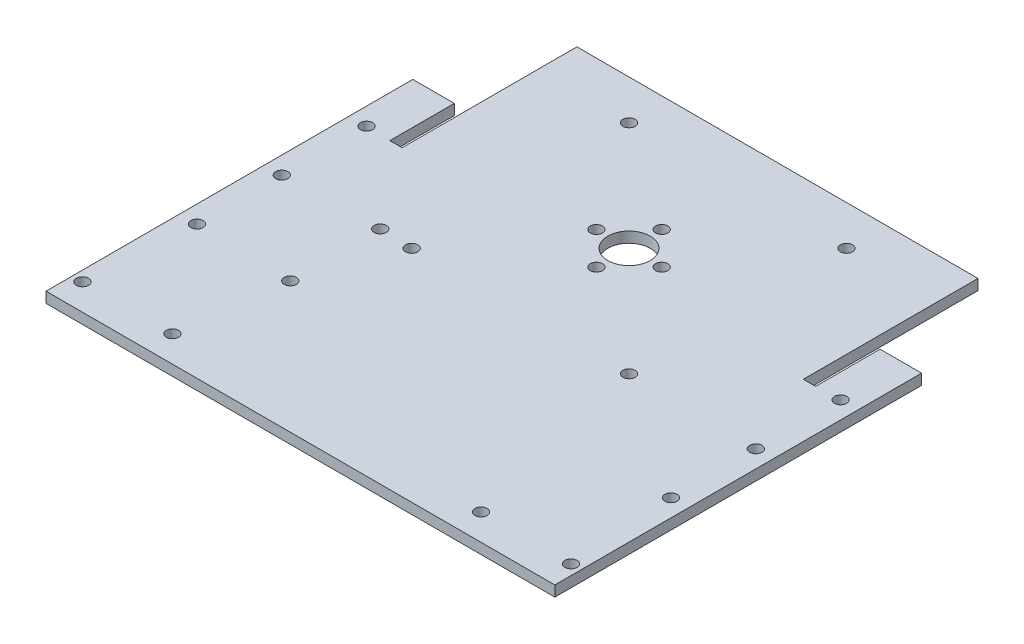
SolidWorks part; units mm, degrees
ref_plane "Front" through (0, 0, 0) normal (0, 0, 1) x (1, 0, 0)
ref_plane "Top" through (0, 0, 0) normal (0, 1, 0) x (1, 0, 0)
ref_plane "Right" through (0, 0, 0) normal (1, 0, 0) x (0, 0, -1)
sketch "Sketch1" plane through (0, 0, 0) normal (0, 1, 0) x (1, 0, 0)
  line L1 (76.2, -44.45) -> (-76.2, -44.45)
  line L2 (76.2, -44.45) -> (76.2, 44.45)
  line L3 (76.2, 44.45) -> (-76.2, 44.45)
  line L4 (-76.2, -44.45) -> (-76.2, 44.45)
  line L5 (76.2, -44.45) -> (-76.2, 44.45) construction
  line L6 (76.2, 44.45) -> (-76.2, -44.45) construction
  point P0 (0, 0)
  dimension "D1" = 88.9
  dimension "D2" = 152.4
extrude "Boss-Extrude1" add sketch "Sketch1" along normal blind 3.175
sketch "Sketch2" plane through (0, 3.175, 0) normal (0, 1, 0) x (1, 0, 0)
  line L0 (-76.2, 0) -> (76.2, 0) construction
  line L1 (-76.2, 44.45) -> (-76.2, -44.45) construction
  line L2 (76.2, -44.45) -> (76.2, 44.45) construction
  line L3 (0, -44.45) -> (0, 44.45) construction
  line L4 (-76.2, -44.45) -> (76.2, -44.45) construction
  line L5 (76.2, 44.45) -> (-76.2, 44.45) construction
  line L6 (0, 44.45) -> (-60.325, 44.45) construction
  line L7 (60.325, 44.45) -> (63.5, 44.45)
  line L8 (-60.325, 44.45) -> (-63.5, 44.45)
  line L9 (-60.325, 44.45) -> (-60.325, 0)
  line L10 (-60.325, 0) -> (-63.5, 0)
  line L11 (-63.5, 44.45) -> (-63.5, 0)
  line L12 (63.5, 44.45) -> (63.5, 0)
  line L13 (60.325, 0) -> (63.5, 0)
  line L14 (60.325, 44.45) -> (60.325, 0)
  dimension "D1" = 60.325
  dimension "D2" = 3.175
extrude "Cut-Extrude1" cut sketch "Sketch2" against normal through all
sketch "Sketch3" plane through (0, 3.175, 0) normal (0, 1, 0) x (1, 0, 0)
  line L0 (-63.5, 44.45) -> (-66.675, 44.45) construction
  line L1 (-63.5, 44.45) -> (-76.2, 44.45) construction
  line L2 (-66.675, 44.45) -> (-66.675, -44.45) construction
  line L3 (-76.2, -44.45) -> (76.2, -44.45) construction
  line L4 (-66.675, -44.45) -> (-70.993, -44.45) construction
  line L5 (-70.993, -44.45) -> (-70.993, -25.4) construction
  line L6 (-70.993, -25.4) -> (-70.993, 0) construction
  line L7 (-70.993, 0) -> (-70.993, 25.4) construction
  line L8 (0, 44.45) -> (0, -44.45) construction
  line L9 (60.325, 44.45) -> (-60.325, 44.45) construction
  circle A0 centre (-70.993, -25.4) radius 1.8288
  circle A1 centre (-70.993, 0) radius 1.8288
  circle A2 centre (-70.993, 25.4) radius 1.8288
  circle A3 centre (70.993, -25.4) radius 1.8288
  circle A4 centre (70.993, 0) radius 1.8288
  circle A5 centre (70.993, 25.4) radius 1.8288
  dimension "D4" = 3.6576
  dimension "D6" = 3.6576
  dimension "D8" = 3.6576
  dimension "D1" = 3.175
  dimension "D2" = 4.318
  dimension "D3" = 19.05
  dimension "D5" = 25.4
  dimension "D7" = 25.4
extrude "Cut-Extrude2" cut sketch "Sketch3" against normal through all
sketch "Sketch6" plane through (0, 3.175, 0) normal (0, 1, 0) x (1, 0, 0)
  line L0 (-63.5, 0) -> (-60.325, 0)
  line L1 (-63.5, 0) -> (-63.5, 25.4)
  line L2 (-60.325, 0) -> (-60.325, 25.4)
  line L3 (-63.5, 25.4) -> (-60.325, 25.4)
  line L4 (0, 44.45) -> (0, -44.45) construction
  line L5 (60.325, 44.45) -> (-60.325, 44.45) construction
  line L6 (-76.2, -44.45) -> (76.2, -44.45) construction
  line L7 (63.5, 0) -> (60.325, 0)
  line L8 (60.325, 0) -> (60.325, 25.4)
  line L9 (63.5, 25.4) -> (60.325, 25.4)
  line L10 (63.5, 0) -> (63.5, 25.4)
  dimension "D1" = 25.4
extrude "Boss-Extrude2" add sketch "Sketch6" against normal blind 3.175
sketch "Sketch7" plane through (0, 3.175, 0) normal (0, 1, 0) x (1, 0, 0)
  line L27 (-63.754, 44.45) -> (-63.5, 44.45)
  line L28 (-63.5, 44.45) -> (-63.5, 25.4)
  line L29 (-63.5, 25.4) -> (-60.325, 25.4)
  line L30 (-63.754, 44.45) -> (-63.754, 25.146)
  line L31 (-63.754, 25.146) -> (-60.071, 25.146)
  line L32 (-60.071, 25.146) -> (-60.071, 44.45)
  line L33 (-63.754, 44.45) -> (-63.754, 25.146)
  line L34 (-63.754, 25.146) -> (-60.071, 25.146)
  line L35 (-60.071, 25.146) -> (-60.071, 44.45)
  line L36 (-60.325, 25.4) -> (-60.325, 44.45)
  line L37 (-60.325, 44.45) -> (-60.071, 44.45)
  dimension "D1" = 0.254
extrude "Cut-Extrude3" cut sketch "Sketch7" against normal through all
sketch "Sketch8" plane through (0, 3.175, 0) normal (0, 1, 0) x (1, 0, 0)
  line L6 (60.071, 44.45) -> (60.325, 44.45)
  line L7 (60.325, 44.45) -> (60.325, 25.4)
  line L8 (60.325, 25.4) -> (63.5, 25.4)
  line L9 (63.754, 25.146) -> (63.754, 44.45)
  line L10 (60.071, 25.146) -> (63.754, 25.146)
  line L11 (60.071, 44.45) -> (60.071, 25.146)
  line L12 (63.754, 25.146) -> (63.754, 44.45)
  line L13 (60.071, 25.146) -> (63.754, 25.146)
  line L14 (60.071, 44.45) -> (60.071, 25.146)
  line L15 (63.5, 25.4) -> (63.5, 44.45)
  line L16 (63.5, 44.45) -> (63.754, 44.45)
  dimension "D1" = 0.254
extrude "Cut-Extrude4" cut sketch "Sketch8" against normal through all
sketch "Sketch9" plane through (0, 3.175, 0) normal (0, 1, 0) x (1, 0, 0)
  line L0 (-76.2, -44.45) -> (76.2, -44.45)
  line L1 (-76.2, -44.45) -> (-76.2, -65.405)
  line L2 (76.2, -44.45) -> (76.2, -65.405)
  line L3 (-76.2, -65.405) -> (76.2, -65.405)
  dimension "D1" = 20.955
extrude "Boss-Extrude3" add sketch "Sketch9" against normal blind 3.175
sketch "Sketch10" plane through (0, 3.175, 0) normal (0, 1, 0) x (1, 0, 0)
  line L0 (0, 44.45) -> (0, -65.405) construction
  line L1 (60.071, 44.45) -> (-60.071, 44.45) construction
  line L2 (-76.2, -65.405) -> (76.2, -65.405) construction
  line L3 (-76.2, -65.405) -> (-73.1647, -65.405) construction
  line L4 (-73.1647, -65.405) -> (-73.1647, -57.531) construction
  line L5 (-73.1647, -57.531) -> (-46.2153, -57.531) construction
  circle A0 centre (-73.1647, -57.531) radius 1.8288
  circle A1 centre (-46.2153, -57.531) radius 1.8288
  circle A2 centre (46.2153, -57.531) radius 1.8288
  circle A3 centre (73.1647, -57.531) radius 1.8288
  dimension "D4" = 3.6576
  dimension "D5" = 3.6576
  dimension "D1" = 3.0353
  dimension "D2" = 7.874
  dimension "D3" = 26.9494
extrude "Cut-Extrude5" cut sketch "Sketch10" against normal through all
sketch "Sketch11" plane through (0, 3.175, 0) normal (0, 1, 0) x (1, 0, 0)
  line L0 (0, 44.45) -> (0, 33.02) construction
  line L1 (60.071, 44.45) -> (-60.071, 44.45) construction
  line L3 (60.071, -11.43) -> (-60.071, -11.43)
  line L4 (60.071, -11.43) -> (60.071, 77.47)
  line L5 (60.071, 77.47) -> (-60.071, 77.47)
  line L6 (-60.071, -11.43) -> (-60.071, 77.47)
  line L7 (60.071, -11.43) -> (-60.071, 77.47) construction
  line L8 (60.071, 77.47) -> (-60.071, -11.43) construction
  dimension "D1" = 11.43
  dimension "D2" = 88.9
  dimension "D3" = 120.142
extrude "Boss-Extrude4" add sketch "Sketch11" against normal blind 3.175
sketch "Sketch12" plane through (0, 3.175, 0) normal (0, 1, 0) x (1, 0, 0)
  line L0 (0, 77.47) -> (0, 33.02) construction
  line L1 (60.071, 77.47) -> (-60.071, 77.47) construction
  circle A0 centre (0, 33.02) radius 6.35
  dimension "D2" = 12.7
  dimension "D1" = 44.45
extrude "Cut-Extrude6" cut sketch "Sketch12" against normal through all
sketch "Sketch13" plane through (0, 3.175, 0) normal (0, 1, 0) x (1, 0, 0)
  line L5 (-32.5501, 65.5701) -> (32.5501, 0.4699) construction
  line L6 (-32.5501, 0.4699) -> (32.5501, 65.5701) construction
  circle A0 centre (32.5501, 0.4699) radius 1.8288
  circle A1 centre (-32.5501, 0.4699) radius 1.8288
  circle A2 centre (-32.5501, 65.5701) radius 1.8288
  circle A3 centre (32.5501, 65.5701) radius 1.8288
  point P0 (0, 33.02)
  point P1 (0, 33.02)
  point P3 (0, 33.02)
  dimension "D3" = 3.6576
  dimension "D4" = 3.6576
  dimension "D5" = 3.6576
  dimension "D6" = 3.6576
  dimension "D1" = 65.1002
  dimension "D2" = 65.1002
extrude "Cut-Extrude7" cut sketch "Sketch13" against normal through all
sketch "Sketch14" plane through (0, 0, 0) normal (0, -1, 0) x (1, 0, 0)
  line L0 (0, -33.02) -> (0, -23.241) construction
  line L1 (0, -33.02) -> (-9.779, -33.02) construction
  line L2 (0, -33.02) -> (-19.1567, -52.1767) construction
  circle A0 centre (0, -23.241) radius 1.8288
  circle A1 centre (-9.779, -33.02) radius 1.8288
  circle A2 centre (0, -42.799) radius 1.8288
  circle A3 centre (9.779, -33.02) radius 1.8288
  dimension "D3" = 3.6576
  dimension "D4" = 3.6576
  dimension "D1" = 9.779
  dimension "D2" = 9.779
extrude "Cut-Extrude8" cut sketch "Sketch14" against normal blind 101.6
sketch "Sketch15" plane through (0, 0, 0) normal (0, -1, 0) x (1, 0, 0)
  line L0 (-76.2, 65.405) -> (-42.291, 65.405) construction
  line L1 (-76.2, 65.405) -> (76.2, 65.405) construction
  line L2 (-42.291, 65.405) -> (-42.291, 26.162) construction
  line L3 (-42.291, 26.162) -> (-42.291, -0.7874) construction
  circle A0 centre (-42.291, 26.162) radius 1.8288
  circle A1 centre (-42.291, -0.7874) radius 1.8288
  dimension "D4" = 3.6576
  dimension "D5" = 3.6576
  dimension "D1" = 33.909
  dimension "D2" = 39.243
  dimension "D3" = 26.9494
extrude "Cut-Extrude9" cut sketch "Sketch15" against normal through all
